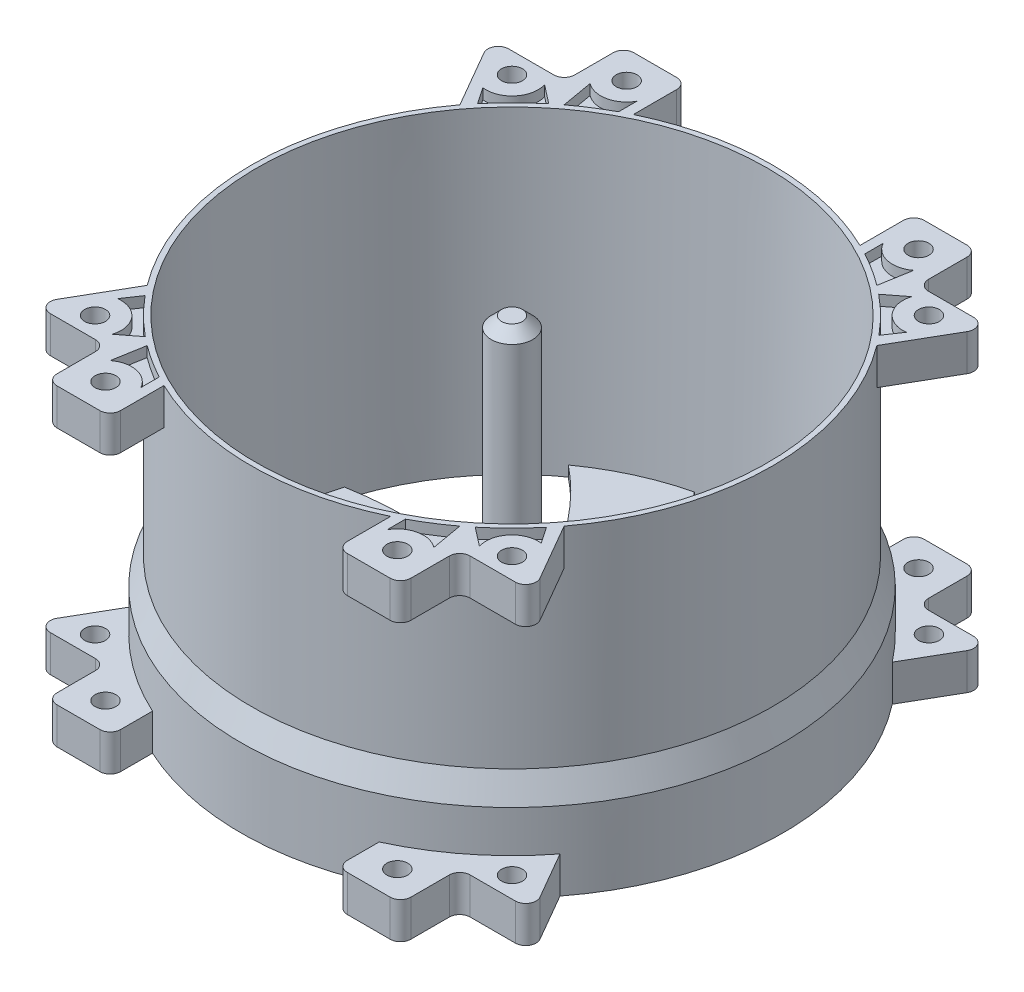
SolidWorks part; units mm, degrees
ref_plane "Front" through (0, 0, 0) normal (0, 0, 1) x (1, 0, 0)
ref_plane "Top" through (0, 0, 0) normal (0, 1, 0) x (1, 0, 0)
ref_plane "Right" through (0, 0, 0) normal (1, 0, 0) x (0, 0, -1)
sketch "Sketch1" plane through (0, 0, 0) normal (0, 0, 1) x (1, 0, 0)
  line L0 (0, 0) -> (0, 34.7876) construction
  line L1 (0, 0) -> (42.0849, 0) construction
  line L2 (0, 0) -> (-65.0965, 0) construction
  line L3 (-24.5, 30) -> (-25, 30)
  line L4 (-25, 30) -> (-25, 10)
  line L5 (-25, 10) -> (-26, 7.5)
  line L6 (-26, 7.5) -> (-26, 0)
  line L7 (-26, 0) -> (-23.75, 0)
  line L8 (-23.75, 0) -> (-24, 10)
  line L9 (-24, 10) -> (-24.5, 30)
  point P7 (-24.75, 30)
  dimension "D1" = 10
  dimension "D2" = 7.5
  dimension "D3" = 30
  dimension "D4" = 24.5
  dimension "D5" = 24
  dimension "D7" = 25
  dimension "D8" = 26
revolve "Revolve1" add sketch "Sketch1" angle 360 about L0
sketch "Sketch2" plane through (0, 0, 0) normal (0, 1, 0) x (1, 0, 0)
  line L0 (0, 24.8193) -> (0, -24.9882) construction
  line L1 (0, 0) -> (131.9419, 0) construction
  line L2 (-3, 24.8193) -> (3, 24.8193)
  arc A0 (-3, 24.8193) -> (3, 24.8193) centre (0, 21.5983) cw
  dimension "D1" = 6
extrude "Boss-Extrude1" [suppressed] add sketch "Sketch2" along normal up to surface (30 mm away) contours L2 A0
pattern_circular "CirPattern1" [suppressed] count 12 over 360
sketch "Sketch3" plane through (0, 0, 0) normal (0, 1, 0) x (1, 0, 0)
  line L0 (0, 0) -> (0, 30.9838) construction
  line L1 (0, 0) -> (-15.6052, 0) construction
  line L2 (0, 0) -> (-20, 20) construction
  line L3 (0, 0) -> (-14, 25) construction
  line L4 (-10.8727, 22.5119) -> (-10.8727, 26.6726)
  line L5 (-11.8727, 27.6726) -> (-15.9758, 27.6726)
  line L6 (-16.9758, 26.6726) -> (-16.9758, 22.9895)
  line L7 (-17.9758, 21.9895) -> (-22.3034, 21.9895)
  line L8 (-23.1694, 20.4895) -> (-20, 15)
  circle A0 centre (-14, 25) radius 1
  circle A1 centre (-20, 20) radius 1
  arc A6 (-22.3034, 21.9895) -> (-23.1694, 20.4895) centre (-22.3034, 20.9895) ccw
  arc A7 (-16.9758, 22.9895) -> (-17.9758, 21.9895) centre (-17.9758, 22.9895) cw
  arc A8 (-15.9758, 27.6726) -> (-16.9758, 26.6726) centre (-15.9758, 26.6726) ccw
  arc A9 (-10.8727, 26.6726) -> (-11.8727, 27.6726) centre (-11.8727, 26.6726) ccw
  arc A10 (-20, 15) -> (-10.8727, 22.5119) centre (0, 0) cw
  dimension "D5" = 2
  dimension "D6" = 60
  dimension "D1" = 20
  dimension "D3" = 14
  dimension "D4" = 25
  dimension "D7" = 1
  dimension "D2" = 20
extrude "Boss-Extrude2" add sketch "Sketch3" along normal blind 3.5
mirror "Mirror1" about plane through (0, 0, 0) normal (1, 0, 0) of "Boss-Extrude2"
mirror "Mirror2" about plane through (0, 0, 0) normal (0, 0, 1) of "Mirror1", "Boss-Extrude2"
ref_plane "Plane1" through (0, 15, 0) normal (0, -1, 0) x (-1, 0, 0)
mirror "Mirror3" about plane through (0, 15, 0) normal (0, -1, 0) of "Mirror2", "Boss-Extrude2", "Mirror1"
sketch "Sketch4" plane through (0, 30, 0) normal (0, 1, 0) x (1, 0, 0)
  line L0 (-19.2517, 15.949) -> (-20.3143, 17.5198)
  line L1 (-11.811, 22.0341) -> (-11.811, 23.7924)
  line L2 (-17.6112, 20.7373) -> (-15.8266, 19.3525)
  line L5 (-15.5215, 23.0163) -> (-15, 20)
  arc A0 (-11.811, 22.0341) -> (-15, 20) centre (0, 0) ccw
  circle A2 centre (0, 0) radius 25 construction
  circle A5 centre (-14, 25) radius 2.5
  arc A6 (-15.5215, 23.0163) -> (-11.811, 23.7924) centre (-14, 25) ccw
  arc A7 (-15.8266, 19.3525) -> (-19.2517, 15.949) centre (0, 0) ccw
  circle A8 centre (-20, 20) radius 2.5
  arc A9 (-20.3143, 17.5198) -> (-17.6112, 20.7373) centre (-20, 20) ccw
  dimension "D1" = 1.5
  dimension "D2" = 1.5
extrude "Cut-Extrude1" cut sketch "Sketch4" against normal blind 1
mirror "Mirror4" about plane through (0, 0, 0) normal (0, 0, 1) of "Cut-Extrude1"
mirror "Mirror5" about plane through (0, 0, 0) normal (1, 0, 0) of "Mirror4", "Cut-Extrude1"
mirror "Mirror7" about plane through (0, 15, 0) normal (0, -1, 0) of "Mirror5", "Cut-Extrude1", "Mirror4"
sketch "Sketch5" plane through (0, 0, 0) normal (0, -1, 0) x (1, 0, 0)
  arc A0 (-4.1801, 1.522) -> (-4.3298, 1.0213) centre (0, 0) ccw
  circle A1 centre (0, 0) radius 23.75 construction
  arc A2 (-9.7546, 21.6543) -> (-17.1965, 16.3812) centre (0, 0) ccw
  arc A3 (-0.772, 4.3811) -> (-1.2804, 4.2603) centre (0, 0) ccw
  arc A4 (3.4081, 2.8591) -> (3.0493, 3.239) centre (0, 0) ccw
  arc A5 (4.1801, -1.522) -> (4.3298, -1.0213) centre (0, 0) ccw
  arc A6 (-3.4081, -2.8591) -> (-3.0493, -3.239) centre (0, 0) ccw
  arc A7 (0.772, -4.3811) -> (1.2804, -4.2603) centre (0, 0) ccw
  arc A8 (13.8759, 19.2749) -> (5.5882, 23.0832) centre (0, 0) ccw
  arc A9 (23.6305, -2.3794) -> (22.7848, 6.7021) centre (0, 0) ccw
  arc A10 (9.7546, -21.6543) -> (17.1965, -16.3812) centre (0, 0) ccw
  arc A11 (-13.8759, -19.2749) -> (-5.5882, -23.0832) centre (0, 0) ccw
  arc A12 (-23.6305, 2.3794) -> (-22.7848, -6.7021) centre (0, 0) ccw
  spline S0 degree 3 poles (-0.772, 4.3811) (-1.3809, 11.0708) (0.7392, 17.3049) (5.5882, 23.0832) knots 0.177053 0.177053 0.177053 0.177053 1 1 1 1
  spline S1 degree 3 poles (3.0493, 3.239) (3.3806, 4.1299) (5.3847, 9.1087) (8.8536, 14.7869) (12.9526, 18.5378) (13.8759, 19.2749) knots 0.186903 0.186903 0.186903 0.186903 0.300339 0.824971 0.966226 0.966226 0.966226 0.966226
  spline S2 degree 3 poles (3.4081, 2.8591) (8.8972, 6.7313) (15.356, 8.0123) (22.7848, 6.7021) knots 0.177053 0.177053 0.177053 0.177053 1 1 1 1
  spline S3 degree 3 poles (4.3298, -1.0213) (5.2669, -0.8627) (10.5808, -0.109) (17.2326, -0.274) (22.5305, -1.9484) (23.6305, -2.3794) knots 0.186903 0.186903 0.186903 0.186903 0.300339 0.824971 0.966226 0.966226 0.966226 0.966226
  spline S4 degree 3 poles (4.1801, -1.522) (10.2781, -4.3395) (14.6169, -9.2926) (17.1965, -16.3812) knots 0.177053 0.177053 0.177053 0.177053 1 1 1 1
  spline S5 degree 3 poles (1.2804, -4.2603) (1.8863, -4.9927) (5.196, -9.2177) (8.3791, -15.0609) (9.5779, -20.4861) (9.7546, -21.6543) knots 0.186903 0.186903 0.186903 0.186903 0.300339 0.824971 0.966226 0.966226 0.966226 0.966226
  spline S6 degree 3 poles (0.772, -4.3811) (1.3809, -11.0708) (-0.7392, -17.3049) (-5.5882, -23.0832) knots 0.177053 0.177053 0.177053 0.177053 1 1 1 1
  spline S7 degree 3 poles (-3.0493, -3.239) (-3.3806, -4.1299) (-5.3847, -9.1087) (-8.8536, -14.7869) (-12.9526, -18.5378) (-13.8759, -19.2749) knots 0.186903 0.186903 0.186903 0.186903 0.300339 0.824971 0.966226 0.966226 0.966226 0.966226
  spline S8 degree 3 poles (-3.4081, -2.8591) (-8.8972, -6.7313) (-15.356, -8.0123) (-22.7848, -6.7021) knots 0.177053 0.177053 0.177053 0.177053 1 1 1 1
  spline S9 degree 3 poles (-4.3298, 1.0213) (-5.2669, 0.8627) (-10.5808, 0.109) (-17.2326, 0.274) (-22.5305, 1.9484) (-23.6305, 2.3794) knots 0.186903 0.186903 0.186903 0.186903 0.300339 0.824971 0.966226 0.966226 0.966226 0.966226
  spline S10 degree 3 poles (-4.1801, 1.522) (-10.2781, 4.3395) (-14.6169, 9.2926) (-17.1965, 16.3812) knots 0.177053 0.177053 0.177053 0.177053 1 1 1 1
  spline S11 degree 3 poles (-1.2804, 4.2603) (-1.8863, 4.9927) (-5.196, 9.2177) (-8.3791, 15.0609) (-9.5779, 20.4861) (-9.7546, 21.6543) knots 0.186903 0.186903 0.186903 0.186903 0.300339 0.824971 0.966226 0.966226 0.966226 0.966226
  point P50 (0, 0)
extrude "Boss-Extrude3" add sketch "Sketch5" against normal blind 1 separate body
sketch "Sketch7" plane through (0, 1, 0) normal (0, 1, 0) x (1, 0, 0)
  circle A0 centre (0, 0) radius 2.5
  dimension "D1" = 5
extrude "Boss-Extrude4" add sketch "Sketch7" along normal blind 10
sketch "Sketch8" plane through (0, 11, 0) normal (0, 1, 0) x (1, 0, 0)
  circle A0 centre (0, 0) radius 2
  dimension "D1" = 4
extrude "Boss-Extrude5" add sketch "Sketch8" along normal up to surface (19 mm away)
chamfer "Chamfer1" distance 1 angle 45 1 edges at (0, 30, -2)
equation "\"inlet_diameter\"= 30"
equation "\"total_length\"=200"
equation "\"outlet_length\"=80"
equation "\"outlet_diameter\"= 50"
equation "\"side_length\"=115"
equation "\"inlet_lentgh\"=80"
equation "\"flat_length\"=120"
equation "\"side_height\"=55"
equation "\"D7@Sketch1\"=\"outlet_diameter\"/2"
equation "\"D4@Sketch1\"=\"outlet_diameter\"/2-0.5"
equation "\"D5@Sketch1\"=\"outlet_diameter\"/2-1"
equation "\"D8@Sketch1\"=\"outlet_diameter\"/2+1"
